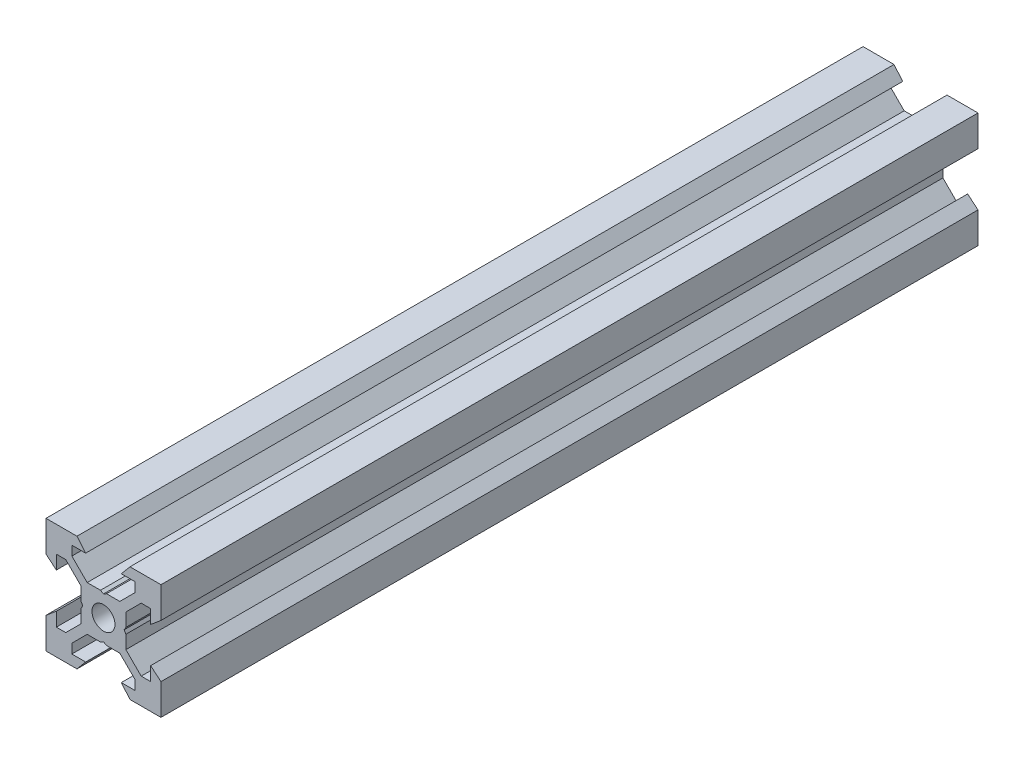
SolidWorks part; units mm, degrees
ref_plane "Front Plane" through (0, 0, 0) normal (0, 0, 1) x (1, 0, 0)
ref_plane "Top Plane" through (0, 0, 0) normal (0, 1, 0) x (1, 0, 0)
ref_plane "Right Plane" through (0, 0, 0) normal (1, 0, 0) x (0, 0, -1)
sketch "Sketch1" plane through (0, 0, 0) normal (0, 0, 1) x (1, 0, 0)
  line L0 (10, 10) -> (4.6104, 10) construction
  line L1 (10, 10) -> (10, 4.6104) construction
  line L2 (10, -10) -> (10, -4.6104) construction
  line L3 (10, -10) -> (4.6104, -10) construction
  line L4 (10, 10) -> (10, 4.6104)
  line L5 (6.5607, 5.5) -> (8.2, 5.5)
  line L6 (5.5, 8.2) -> (5.5, 6.5607)
  line L7 (10, 10) -> (4.6104, 10)
  line L8 (10, 10) -> (10, 4.6104)
  line L9 (6.5607, 5.5) -> (3.9, 2.8393)
  line L10 (5.5, 6.5607) -> (2.8393, 3.9)
  line L11 (10, 4.6104) -> (8.2, 3.1)
  line L12 (4.6104, 10) -> (3.1, 8.2)
  line L13 (8.2, 3.1) -> (8.2, 5.5)
  line L14 (3.1, 8.2) -> (5.5, 8.2)
  line L15 (-6.5607, 5.5) -> (-8.2, 5.5)
  line L16 (6.5607, -5.5) -> (8.2, -5.5)
  line L17 (3.1, -8.2) -> (5.5, -8.2)
  line L18 (8.2, -3.1) -> (8.2, -5.5)
  line L19 (4.6104, -10) -> (3.1, -8.2)
  line L20 (10, -4.6104) -> (8.2, -3.1)
  line L21 (0.5196, -3.9) -> (0, -3.6)
  line L22 (0.5196, 3.9) -> (0, 3.6)
  line L23 (3.6, 0) -> (3.9, -0.5196)
  line L24 (3.9, 0.5196) -> (3.6, 0)
  line L25 (3.9, 0.5196) -> (3.9, 2.8393)
  line L26 (2.8393, 3.9) -> (0.5196, 3.9)
  line L27 (3.9, -2.8393) -> (3.9, -0.5196)
  line L28 (2.8393, -3.9) -> (0.5196, -3.9)
  line L29 (5.5, -6.5607) -> (2.8393, -3.9)
  line L30 (6.5607, -5.5) -> (3.9, -2.8393)
  line L31 (10, -10) -> (10, -4.6104)
  line L32 (10, -10) -> (4.6104, -10)
  line L33 (5.5, -8.2) -> (5.5, -6.5607)
  line L34 (-6.5607, -5.5) -> (-8.2, -5.5)
  line L35 (10, -10) -> (10, -4.6104)
  line L36 (0, 0) -> (0, 8.2) construction
  line L37 (-10, -10) -> (-4.6104, -10) construction
  line L38 (-10, -10) -> (-10, -4.6104) construction
  line L39 (-10, 10) -> (-10, 4.6104) construction
  line L40 (-10, 10) -> (-4.6104, 10) construction
  line L41 (-10, -10) -> (-10, -4.6104)
  line L43 (-5.5, -8.2) -> (-5.5, -6.5607)
  line L44 (-10, -10) -> (-4.6104, -10)
  line L45 (-10, -10) -> (-10, -4.6104)
  line L46 (-6.5607, -5.5) -> (-3.9, -2.8393)
  line L47 (-5.5, -6.5607) -> (-2.8393, -3.9)
  line L48 (-2.8393, -3.9) -> (-0.5196, -3.9)
  line L49 (-3.9, -2.8393) -> (-3.9, -0.5196)
  line L50 (-2.8393, 3.9) -> (-0.5196, 3.9)
  line L51 (-3.9, 0.5196) -> (-3.9, 2.8393)
  line L52 (-3.9, 0.5196) -> (-3.6, 0)
  line L53 (-3.6, 0) -> (-3.9, -0.5196)
  line L54 (-0.5196, 3.9) -> (0, 3.6)
  line L55 (-0.5196, -3.9) -> (0, -3.6)
  line L56 (-10, -4.6104) -> (-8.2, -3.1)
  line L57 (-4.6104, -10) -> (-3.1, -8.2)
  line L58 (-8.2, -3.1) -> (-8.2, -5.5)
  line L59 (-3.1, -8.2) -> (-5.5, -8.2)
  line L60 (-10, -10) -> (10, -10) construction
  line L61 (-10, -10) -> (-10, 10) construction
  line L62 (-3.1, 8.2) -> (-5.5, 8.2)
  line L63 (-8.2, 3.1) -> (-8.2, 5.5)
  line L64 (-4.6104, 10) -> (-3.1, 8.2)
  line L65 (-10, 4.6104) -> (-8.2, 3.1)
  line L66 (-5.5, 6.5607) -> (-2.8393, 3.9)
  line L67 (-6.5607, 5.5) -> (-3.9, 2.8393)
  line L68 (-10, 10) -> (-10, 4.6104)
  line L69 (-10, 10) -> (-4.6104, 10)
  line L70 (-5.5, 8.2) -> (-5.5, 6.5607)
  line L71 (-10, 10) -> (10, 10) construction
  line L72 (-10, 10) -> (-10, 4.6104)
  line L73 (10, -10) -> (10, 10) construction
  line L74 (-10, -10) -> (10, 10) construction
  line L75 (-10, 10) -> (10, -10) construction
  circle A0 centre (0, 0) radius 2
  dimension "D7" = 4
  dimension "D1" = 20
  dimension "D2" = 5.3896
  dimension "D3" = 4.5
  dimension "D4" = 50
  dimension "D5" = 1.8
  dimension "D6" = 1.5104
  dimension "D8" = 5.5
  dimension "D9" = 120
  dimension "D10" = 0.3
  dimension "D11" = 2.3197
  dimension "D12" = 7.8
  dimension "D13" = 7.8
  dimension "D14" = 1.5
  dimension "D15" = 2.6607
extrude "Boss-Extrude1" add sketch "Sketch1" along normal mid plane 142.15 contours L70 L62 L64 L69 L68 L65 L63 L15 L67 L51 L52 L53 L49 L46 L34 L58 L56 L41 L44 L57 L59 L43 L47 L48 L55 L21 L28 L29 L33 L17 L19 L32 L31 L20 L18 L16 L30 L27 L23 L24 L25 L9 L5 L13 L11 L4 L7 L12 L14 L6 L10
